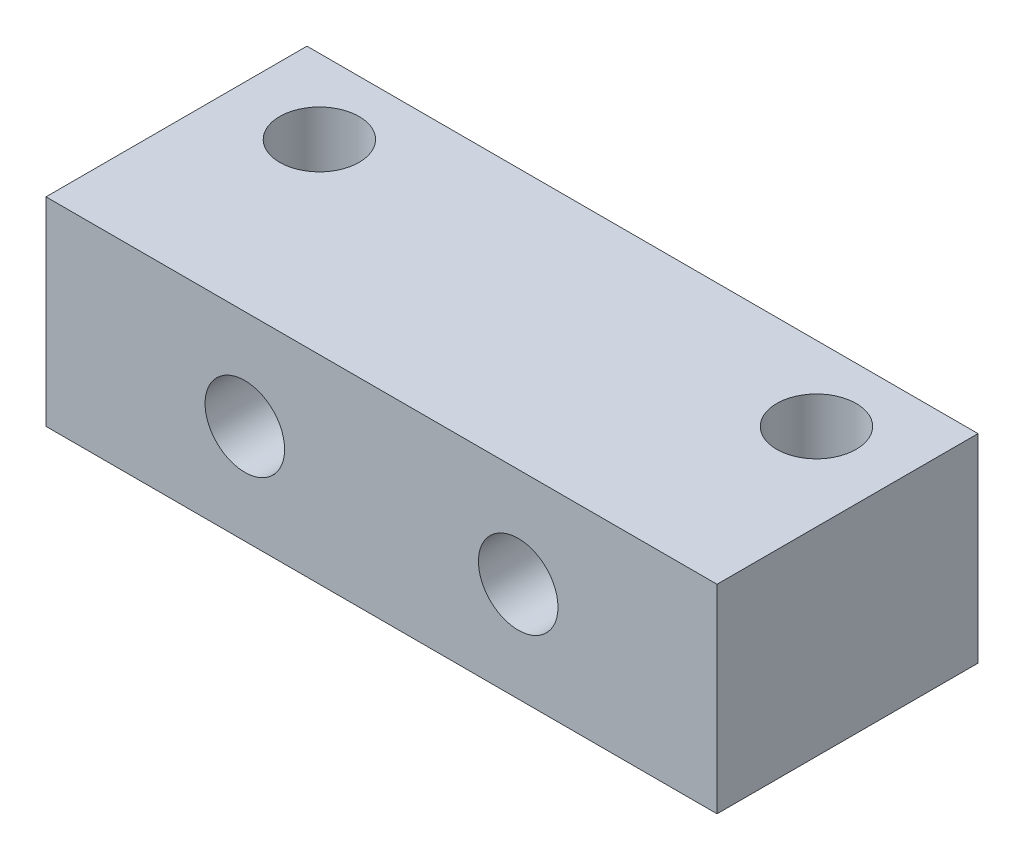
SolidWorks part; units mm, degrees
ref_plane "Front Plane" through (0, 0, 0) normal (0, 0, 1) x (1, 0, 0)
ref_plane "Top Plane" through (0, 0, 0) normal (0, 1, 0) x (1, 0, 0)
ref_plane "Right Plane" through (0, 0, 0) normal (1, 0, 0) x (0, 0, -1)
sketch "Sketch1" plane through (0, 0, 0) normal (0, 1, 0) x (1, 0, 0)
  line L0 (0, 0) -> (20, 0) construction
  line L2 (-3.5, -3) -> (23.5, -3)
  line L3 (-3.5, -3) -> (-3.5, 3)
  line L4 (-3.5, 3) -> (23.5, 3)
  line L5 (23.5, -3) -> (23.5, 3)
  line L6 (-3.5, -3) -> (23.5, 3) construction
  line L7 (-3.5, 3) -> (23.5, -3) construction
  circle A0 centre (0, 0) radius 1.6
  circle A1 centre (20, 0) radius 1.6
  point P5 (10, 0)
  dimension "D1" = 3.2
  dimension "D3" = 6
  dimension "D2" = 20
  dimension "D4" = 27
extrude "Boss-Extrude1" add sketch "Sketch1" along normal blind 8
sketch "Sketch3" plane through (0, 0, 3) normal (0, 0, 1) x (1, 0, 0)
  line L1 (-3.5, 0) -> (23.5, 0)
  line L2 (-3.5, 0) -> (-3.5, 8)
  line L3 (-3.5, 8) -> (23.5, 8)
  line L4 (23.5, 0) -> (23.5, 8)
extrude "Boss-Extrude2" add sketch "Sketch3" along normal blind 4.5
sketch "Sketch2" plane through (0, 0, 0) normal (0, 0, 1) x (1, 0, 0)
  line L0 (4.5, 8) -> (4.5, 0) construction
  line L3 (4.5, 4) -> (15.5, 4) construction
  line L4 (10, 0) -> (10, 8) construction
  line L5 (23.5, 8) -> (-3.5, 8) construction
  line L6 (-3.5, 0) -> (23.5, 0) construction
  circle A0 centre (4.5, 4) radius 1.6
  circle A1 centre (15.5, 4) radius 1.6
  point P8 (0, 0)
  point P12 (0, 0)
  point P13 (10, 4)
  point P15 (0, 0)
  point P16 (0, 0)
  point P17 (0, 0)
  point P18 (0, 0)
  dimension "D1" = 11
  dimension "D2" = 3.2
extrude "Cut-Extrude1" cut sketch "Sketch2" against normal through all both and the other way through all contours A0 | A1
